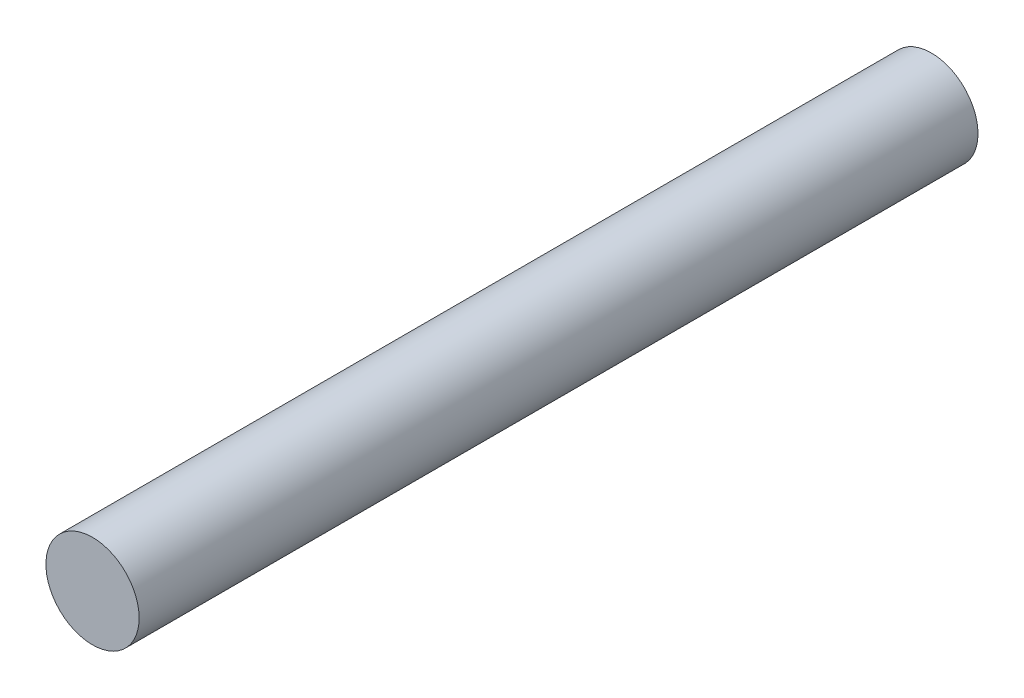
SolidWorks part; units mm, degrees
ref_plane "Front Plane" through (0, 0, 0) normal (0, 0, 1) x (1, 0, 0)
ref_plane "Top Plane" through (0, 0, 0) normal (0, 1, 0) x (1, 0, 0)
ref_plane "Right Plane" through (0, 0, 0) normal (1, 0, 0) x (0, 0, -1)
sketch "Sketch1" plane through (0, 0, 0) normal (0, 0, 1) x (1, 0, 0)
  circle A0 centre (0, 0) radius 2.5
  dimension "D1" = 5
extrude "Boss-Extrude1" add sketch "Sketch1" against normal blind 45
